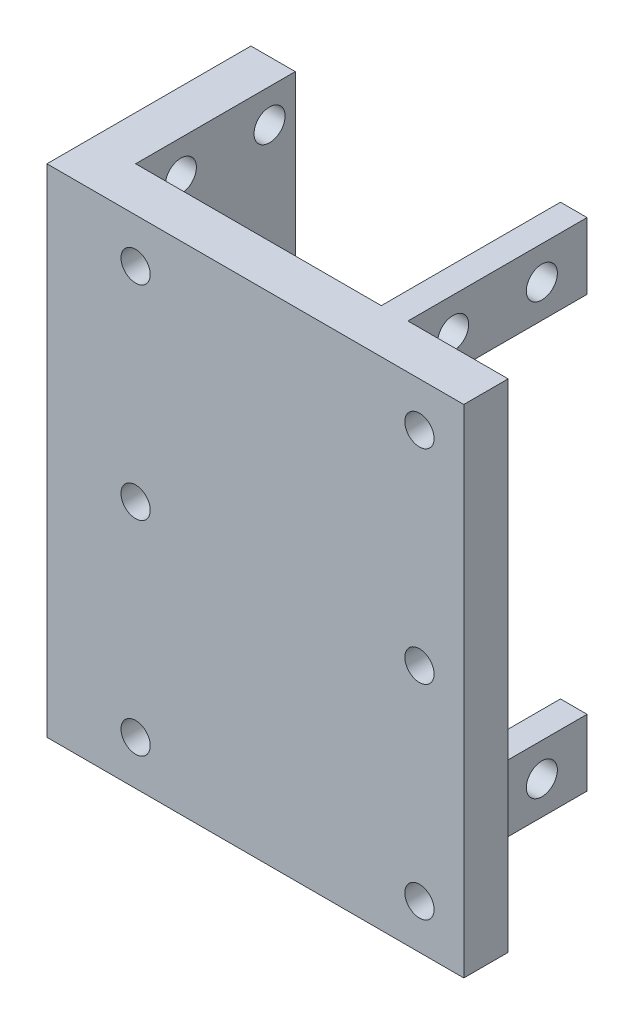
SolidWorks part; units mm, degrees
ref_plane "Front" through (0, 0, 0) normal (0, 0, 1) x (1, 0, 0)
ref_plane "Top" through (0, 0, 0) normal (0, 1, 0) x (1, 0, 0)
ref_plane "Right" through (0, 0, 0) normal (1, 0, 0) x (0, 0, -1)
sketch "草图1" plane through (0, 0, 0) normal (0, 0, 1) x (1, 0, 0)
  line L1 (-21, -28) -> (21, -28)
  line L2 (-21, -28) -> (-21, 28)
  line L3 (-21, 28) -> (21, 28)
  line L4 (21, -28) -> (21, 28)
  line L5 (0, 28) -> (0, -28) construction
  line L6 (-21, 0) -> (21, 0) construction
  point P0 (0, 0)
  dimension "D1" = 56
  dimension "D2" = 42
extrude "凸台-拉伸1" add sketch "草图1" along normal blind 5
sketch "草图2" plane through (0, 0, 5) normal (0, 0, 1) x (1, 0, 0)
  line L0 (-21, 28) -> (-21, -28) construction
  line L1 (-21, 28) -> (-21, -28) construction
  line L3 (-26, -28) -> (-21, -28)
  line L4 (-26, -28) -> (-26, 28)
  line L5 (-26, 28) -> (-21, 28)
  line L6 (-21, -28) -> (-21, 28)
  line L7 (-23.5, 28) -> (-23.5, -28) construction
  line L8 (-26, 0) -> (-21, 0) construction
  point P2 (-23.5, 0)
  dimension "D1" = 5
extrude "凸台-拉伸2" add sketch "草图2" against normal blind 23
sketch "草图3" plane through (0, 0, 0) normal (0, 0, -1) x (-1, 0, 0)
  line L0 (-9.7, 28) -> (-9.7, -28) construction
  line L1 (-21, 28) -> (21, 28) construction
  line L2 (21, -28) -> (-21, -28) construction
  line L3 (-21, -28) -> (-21, 28) construction
  line L4 (-21, -20.5) -> (21, -20.5) construction
  line L5 (21, 28) -> (21, -28) construction
  line L6 (-9.7, -28) -> (-9.7, -20.5)
  line L7 (-9.7, -20.5) -> (-6.7, -20.5)
  line L8 (-6.7, -20.5) -> (-6.7, -28)
  line L9 (-6.7, -28) -> (-9.7, -28)
  line L10 (0, 0) -> (-21, 0) construction
  line L11 (-9.7, 20.5) -> (-6.7, 20.5)
  line L12 (-9.7, 28) -> (-9.7, 20.5)
  line L13 (-6.7, 28) -> (-9.7, 28)
  line L14 (-6.7, 20.5) -> (-6.7, 28)
  dimension "D1" = 27.7
  dimension "D2" = 7.5
  dimension "D3" = 3
extrude "凸台-拉伸3" add sketch "草图3" along normal blind 20.2
sketch "草图4" plane through (9.7, 0, 0) normal (1, 0, 0) x (0, 0, -1)
  line L0 (20.2, 24.25) -> (0, 24.25) construction
  line L1 (20.2, 28) -> (20.2, 20.5) construction
  line L2 (0, -28) -> (0, 28) construction
  line L3 (20.2, 20.5) -> (0, 20.5) construction
  line L4 (10.1, 24.25) -> (10.1, 28) construction
  line L5 (20.2, 28) -> (0, 28) construction
  line L6 (0, 0) -> (18, 0) construction
  line L7 (18, -28) -> (18, 28) construction
  circle A0 centre (5.1, 24.25) radius 1.75
  circle A1 centre (15.1, 24.25) radius 1.75
  circle A2 centre (15.1, -24.25) radius 1.75
  circle A3 centre (5.1, -24.25) radius 1.75
  dimension "D2" = 3.5
  dimension "D1" = 3.75
  dimension "D3" = 10
extrude "切除-拉伸1" cut sketch "草图4" against normal through all
sketch "草图5" plane through (0, 0, 0) normal (0, 0, -1) x (-1, 0, 0)
  line L0 (-21, -28) -> (-21, 28) construction
  line L1 (-21, 28) -> (-9.7, 28) construction
  line L2 (-21, 0) -> (21, 0) construction
  line L3 (21, -28) -> (21, 28) construction
  line L4 (0, 28) -> (0, -28) construction
  line L5 (-6.7, 28) -> (21, 28) construction
  line L6 (21, -28) -> (-6.7, -28) construction
  line L7 (16, -23) -> (16, 23) construction
  circle A0 centre (-16, 23) radius 1.65
  circle A1 centre (-16, -23) radius 1.65
  circle A2 centre (16, -23) radius 1.65
  circle A3 centre (16, 23) radius 1.65
  circle A4 centre (16, 0) radius 1.65
  circle A5 centre (-16, 0) radius 1.65
  dimension "D1" = 3.3
  dimension "D4" = 3.3
  dimension "D2" = 5
  dimension "D3" = 5
extrude "切除-拉伸2" cut sketch "草图5" against normal blind 10
